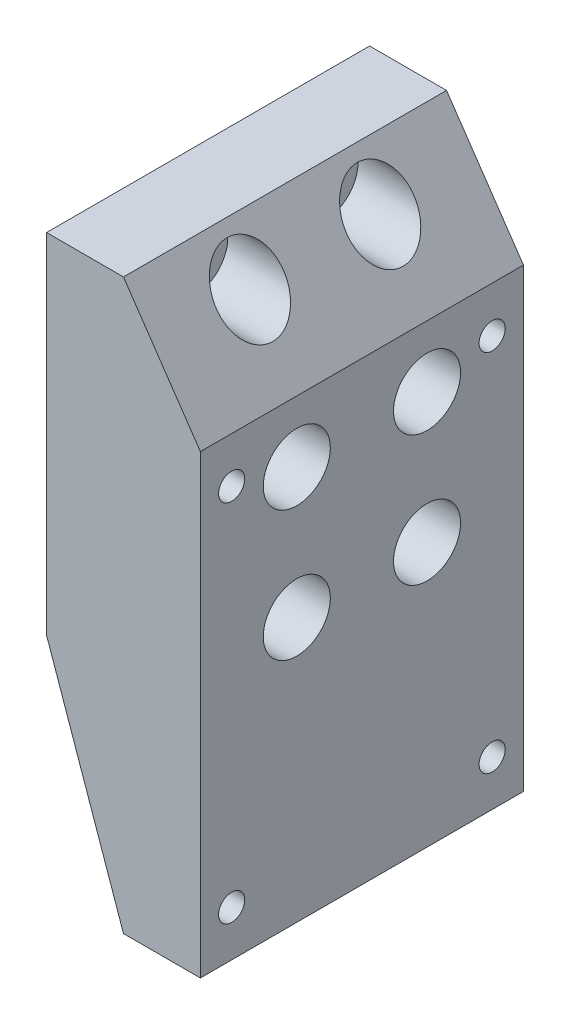
SolidWorks part; units mm, degrees
material "Plain Carbon Steel"
ref_plane "Front Plane" through (0, 0, 0) normal (0, 0, 1) x (1, 0, 0)
ref_plane "Top Plane" through (0, 0, 0) normal (0, 1, 0) x (1, 0, 0)
ref_plane "Right Plane" through (0, 0, 0) normal (1, 0, 0) x (0, 0, -1)
sketch "Sketch1" plane through (0, 0, 0) normal (0, 0, 1) x (1, 0, 0)
  line L0 (-38.7226, 45.3962) -> (-38.7226, -22.6038)
  line L1 (-38.7226, -22.6038) -> (-23.7226, -65.5038)
  line L2 (-23.7226, -65.5038) -> (-8.7226, -65.5038)
  line L3 (-8.7226, -65.5038) -> (-8.7226, 23.3962)
  line L4 (-8.7226, 23.3962) -> (-23.7226, 45.3962)
  line L5 (-23.7226, 45.3962) -> (-38.7226, 45.3962)
  dimension "D1" = 68
  dimension "D2" = 15
  dimension "D3" = 15
  dimension "D4" = 88.9
  dimension "D5" = 22
  dimension "D6" = 30
extrude "Boss-Extrude1" add sketch "Sketch1" along normal blind 63
sketch "Sketch2" plane through (-38.7226, 0, 0) normal (-1, 0, 0) x (0, 0, 1)
  line L0 (31.5, 45.3962) -> (31.5, -22.6038) construction
  line L1 (63, 45.3962) -> (0, 45.3962) construction
  line L2 (63, -22.6038) -> (0, -22.6038) construction
  line L3 (0, 11.3962) -> (63, 11.3962) construction
  line L4 (0, 45.3962) -> (0, -22.6038) construction
  line L5 (63, 45.3962) -> (63, -22.6038) construction
  point P12 (31.5, 11.3962)
  point P13 (18.8, 36.7962)
  point P14 (31.5, 45.3962)
  point P15 (0, 11.3962)
  point P16 (63, 11.3962)
  point P17 (31.5, -22.6038)
  point P18 (44.2, 36.7962)
  point P19 (31.5, 24.0962)
  point P20 (56.9, 24.0962)
  point P21 (6.1, 24.0962)
  point P22 (18.8, 11.3962)
  point P23 (44.2, 11.3962)
  point P24 (6.1, -1.3038)
  point P25 (31.5, -1.3038)
  point P26 (56.9, -1.3038)
  point P27 (18.8, -14.0038)
  point P28 (44.2, -14.0038)
  dimension "D1" = 8.6
  dimension "D2" = 12.7
  dimension "D3" = 8.6
  dimension "D4" = 12.7
  dimension "D5" = 12.7
  dimension "D6" = 25.4
  dimension "D7" = 12.7
  dimension "D8" = 25.4
  dimension "D9" = 12.7
  dimension "D10" = 25.4
  dimension "D11" = 25.4
  dimension "D12" = 25.4
  dimension "D13" = 25.4
  dimension "D14" = 25.4
  dimension "D15" = 25.4
  dimension "D16" = 25.4
sketch "Sketch3" plane through (-38.7226, 0, 0) normal (-1, 0, 0) x (0, 0, 1)
  circle A0 centre (18.8, 36.7962) radius 3.5687
  circle A1 centre (44.2, 36.7962) radius 3.5687
  circle A5 centre (18.8, 11.3962) radius 3.5687
  circle A6 centre (44.2, 11.3962) radius 3.5687
  circle A9 centre (18.8, -14.0038) radius 3.5687
  circle A10 centre (44.2, -14.0038) radius 3.5687
  dimension "D1" = 7.1374
  dimension "D2" = 7.1374
  dimension "D6" = 7.1374
  dimension "D7" = 7.1374
  dimension "D11" = 7.1374
  dimension "D12" = 7.1374
extrude "Cut-Extrude1" cut sketch "Sketch3" against normal blind 63
sketch "Sketch4" plane through (-8.7226, 0, 0) normal (1, 0, 0) x (0, 0, -1)
  circle A0 centre (-44.2, -14.0038) radius 6.5405
  circle A1 centre (-18.8, -14.0038) radius 6.5405
  circle A2 centre (-18.8, 11.3962) radius 6.5405
  circle A4 centre (-44.2, 36.7962) radius 6.5405
  circle A5 centre (-18.8, 36.7962) radius 6.5405
  circle A6 centre (-44.2, 11.3962) radius 6.5405
  dimension "D1" = 13.081
  dimension "D2" = 13.081
  dimension "D3" = 13.081
  dimension "D4" = 13.081
  dimension "D5" = 13.081
  dimension "D6" = 13.081
extrude "Cut-Extrude2" cut sketch "Sketch4" against normal blind 20
sketch "Sketch5" plane through (-8.7226, 0, 0) normal (1, 0, 0) x (0, 0, -1)
  line L0 (-31.5, 23.3962) -> (-31.5, -65.5038) construction
  line L1 (-63, 23.3962) -> (0, 23.3962) construction
  line L2 (-63, -65.5038) -> (0, -65.5038) construction
  line L3 (-63, 23.3962) -> (0, 23.3962) construction
  line L4 (-63, 23.3962) -> (0, 23.3962) construction
  point P6 (-56.9, 14.5062)
  point P7 (-6.1, 14.5062)
  point P12 (-56.9, -56.6138)
  point P13 (-6.1, -56.6138)
  dimension "D1" = 8.89
  dimension "D2" = 8.89
  dimension "D3" = 25.4
  dimension "D4" = 25.4
  dimension "D5" = 8.89
  dimension "D6" = 8.89
hole_wizard "1/4-20 Tapped Hole1" positions "Sketch6" profile "Sketch7" tap size "1/4-20" standard "ANSI Inch"
sketch "Sketch6" plane through (-8.7226, 0, 0) normal (1, 0, 0) x (0, 0, -1)
  point P0 (-56.9, 14.5062)
  point P3 (-6.1, 14.5062)
  point P6 (-56.9, -56.6138)
  point P9 (-6.1, -56.6138)
sketch "Sketch7" plane through (-8.7226, 14.5062, 56.9) normal (0, 1, 0) x (0, 0, -1)
  line L0 (0, 0) -> (0, 11.5338)
  line L1 (0, 11.5338) -> (2.5527, 10)
  line L2 (2.5527, 10) -> (2.5527, 0)
  line L5 (2.5527, 0) -> (0, 0)
  line L10 (0, 11.5338) -> (-2.5527, 10) construction
  line L11 (0, -6.35) -> (0, 107.95) construction
  dimension "Tap Drill Dia." = 5.1054
  dimension "Tap Drill Depth" = 10
  dimension "Drill Angle" = 118
cosmetic thread "Hole Thread1" parameters "D1"=6.1722, "D2"=6.35
cosmetic thread "Hole Thread2" parameters "D1"=6.1722, "D2"=6.35
cosmetic thread "Hole Thread3" parameters "D1"=6.1722, "D2"=6.35
cosmetic thread "Hole Thread4" parameters "D1"=6.1722, "D2"=6.35
